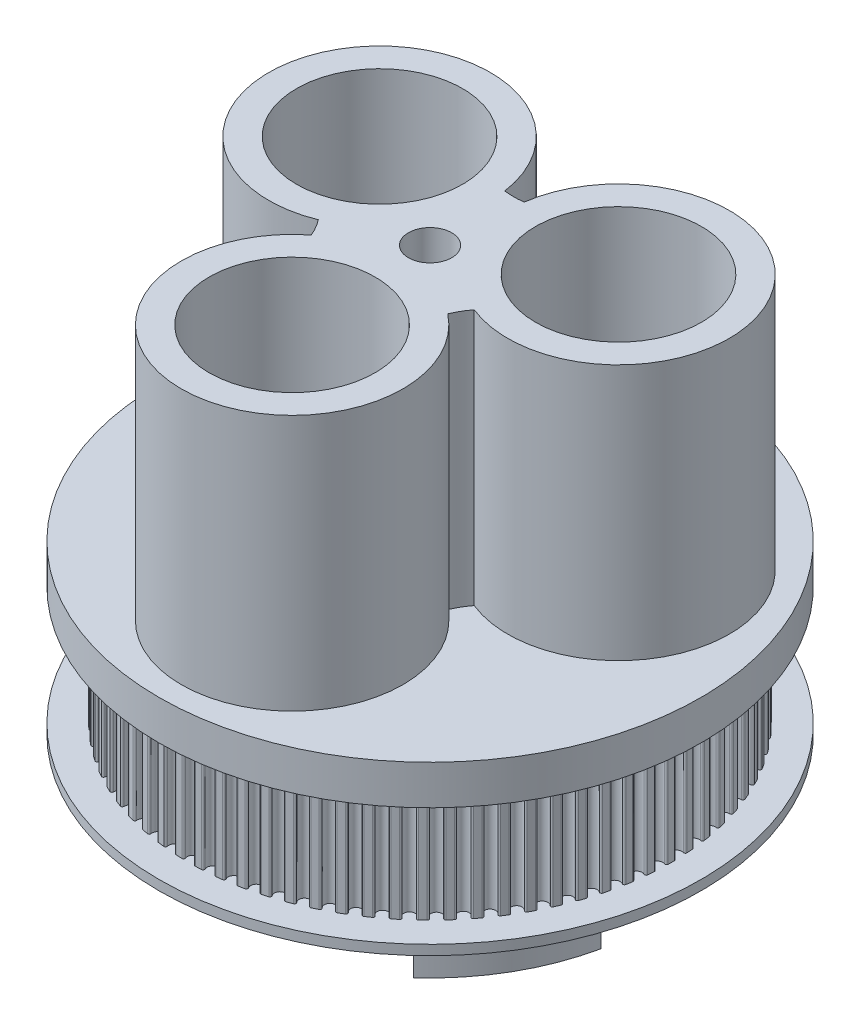
SolidWorks part; units mm, degrees
ref_plane "Front Plane" through (0, 0, 0) normal (0, 0, 1) x (1, 0, 0)
ref_plane "Top Plane" through (0, 0, 0) normal (0, 1, 0) x (1, 0, 0)
ref_plane "Right Plane" through (0, 0, 0) normal (1, 0, 0) x (0, 0, -1)
sketch "Sketch1" plane through (0, 0, 0) normal (0, 1, 0) x (1, 0, 0)
  line L0 (0, -55) -> (0, 55) construction
  circle A0 centre (0, 0) radius 27.5
  circle A1 centre (0, 0) radius 2.2
  circle A2 centre (0, -14) radius 8.425
  circle A3 centre (-12.1244, 7) radius 8.425
  circle A4 centre (12.1244, 7) radius 8.425
  point P14 (0, 0)
  dimension "D1" = 55
  dimension "D2" = 4.4
  dimension "D3" = 16.85
  dimension "D4" = 14
  dimension "D5" = 3
extrude "Boss-Extrude1" add sketch "Sketch1" along normal blind 43
sketch "Sketch4" plane through (0, 0, 0) normal (1, 0, 0) x (0, 0, -1)
  line L0 (-37.5347, 7) -> (42.095, 7) construction
  line L2 (27.5, 0) -> (27.5, 43) construction
  line L3 (27.5, 13) -> (24.5, 13)
  line L4 (27.5, 13) -> (27.5, 1)
  line L5 (27.5, 1) -> (24.5, 1)
  line L6 (24.5, 13) -> (24.5, 1)
  line L7 (0, 27.0195) -> (0, 5.2114) construction
  line L8 (0, 55) -> (0, -55) construction
  line L9 (55, 0) -> (-55, 0) construction
  dimension "D1" = 7
  dimension "D2" = 12
  dimension "D3" = 3
revolve "Cut-Revolve1" cut sketch "Sketch4" angle 360 about L7
sketch "Sketch5" plane through (0, 43, 0) normal (0, 1, 0) x (1, 0, 0)
  line L0 (0, 0) -> (23.3129, -13.4597) construction
  line L1 (0, -55) -> (0, 55) construction
  circle A0 centre (12.1244, 7) radius 11.25
  circle A1 centre (0, 0) radius 30
  circle A2 centre (0, -14) radius 11.25
  circle A3 centre (-12.1244, 7) radius 11.25
  circle A4 centre (13.8564, -8) radius 7.5
  circle A5 centre (-13.8564, -8) radius 7.5
  circle A6 centre (0, 16) radius 7.5
  point P12 (0, 0)
  point P22 (0, 0)
  dimension "D1" = 22.5
  dimension "D2" = 60
  dimension "D5" = 15
  dimension "D4" = 60
  dimension "D6" = 16
  dimension "D3" = 3
  dimension "D7" = 3
extrude "Cut-Extrude3" cut sketch "Sketch5" against normal blind 26
sketch "Sketch6" plane through (0, 0, 0) normal (0, -1, 0) x (1, 0, 0)
  line L0 (0, 0) -> (-24.1185, 13.9248) construction
  line L1 (0, -23.65) -> (0, 23.65) construction
  line L2 (-15.0554, 16.7208) -> (-11.0407, 12.2619)
  line L3 (-22.0083, 4.678) -> (-16.1394, 3.4305)
  line L4 (15.0554, 16.7208) -> (11.0407, 12.2619)
  line L5 (22.0083, 4.678) -> (16.1394, 3.4305)
  line L6 (6.9529, -21.3988) -> (5.0988, -15.6924)
  line L7 (-6.9529, -21.3988) -> (-5.0988, -15.6924)
  circle A0 centre (0, 0) radius 22.5 construction
  circle A1 centre (0, 0) radius 27.5 construction
  circle A2 centre (0, 0) radius 16.5
  circle A3 centre (0, 0) radius 22.5
  point P24 (1.3727, -0.446)
  point P26 (0, 0)
  dimension "D1" = 5
  dimension "D3" = 6
  dimension "D2" = 60
  dimension "D4" = 36
  dimension "D5" = 3
extrude "Boss-Extrude2" add sketch "Sketch6" along normal blind 5.5
ref_plane "Plane1" through (0, 13, 0) normal (0, -1, 0) x (-1, 0, 0)
sketch "Sketch9" plane through (0, 13, 0) normal (0, -1, 0) x (-1, 0, 0)
  circle A0 centre (0, 0) radius 24.63 construction
  circle A1 centre (24.0514, -0.9457) radius 0.56
  dimension "D1" = 49.26
  dimension "D2" = 1.12
extrude "Cut-Extrude11" cut sketch "Sketch9" along normal up to surface (12 mm away) up to face at (0, 1, 24.5)
fillet "Fillet1" radius 0.16 2 edges at (-24.4642, 7, 1.3242) (-24.4926, 7, 0.6009)
pattern_circular "CirPattern1" count 78 over 360 about axis through (0, 0, 0) along (0, 1, 0) of "Cut-Extrude11", "Fillet1"
